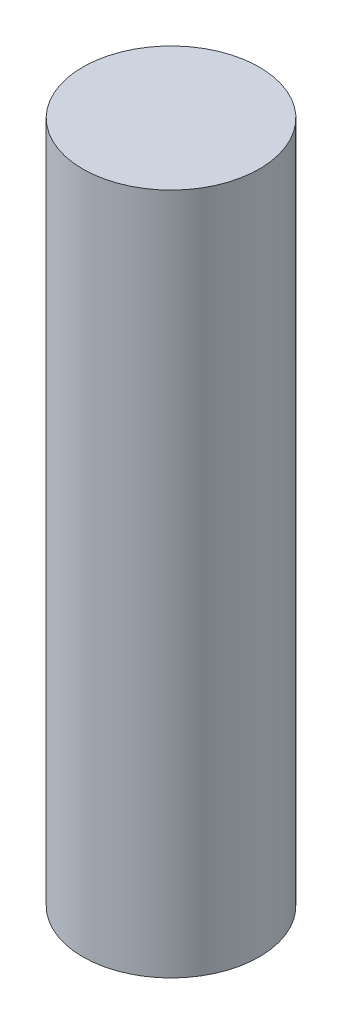
SolidWorks part; units mm, degrees
ref_plane "Front Plane" through (0, 0, 0) normal (0, 0, 1) x (1, 0, 0)
ref_plane "Top Plane" through (0, 0, 0) normal (0, 1, 0) x (1, 0, 0)
ref_plane "Right Plane" through (0, 0, 0) normal (1, 0, 0) x (0, 0, -1)
sketch "Sketch3" plane through (0, 0, 0) normal (0, 1, 0) x (1, 0, 0)
  circle A1 centre (0, 0) radius 11
extrude "Boss-Extrude5" add sketch "Sketch3" along normal blind 85 contours A1
